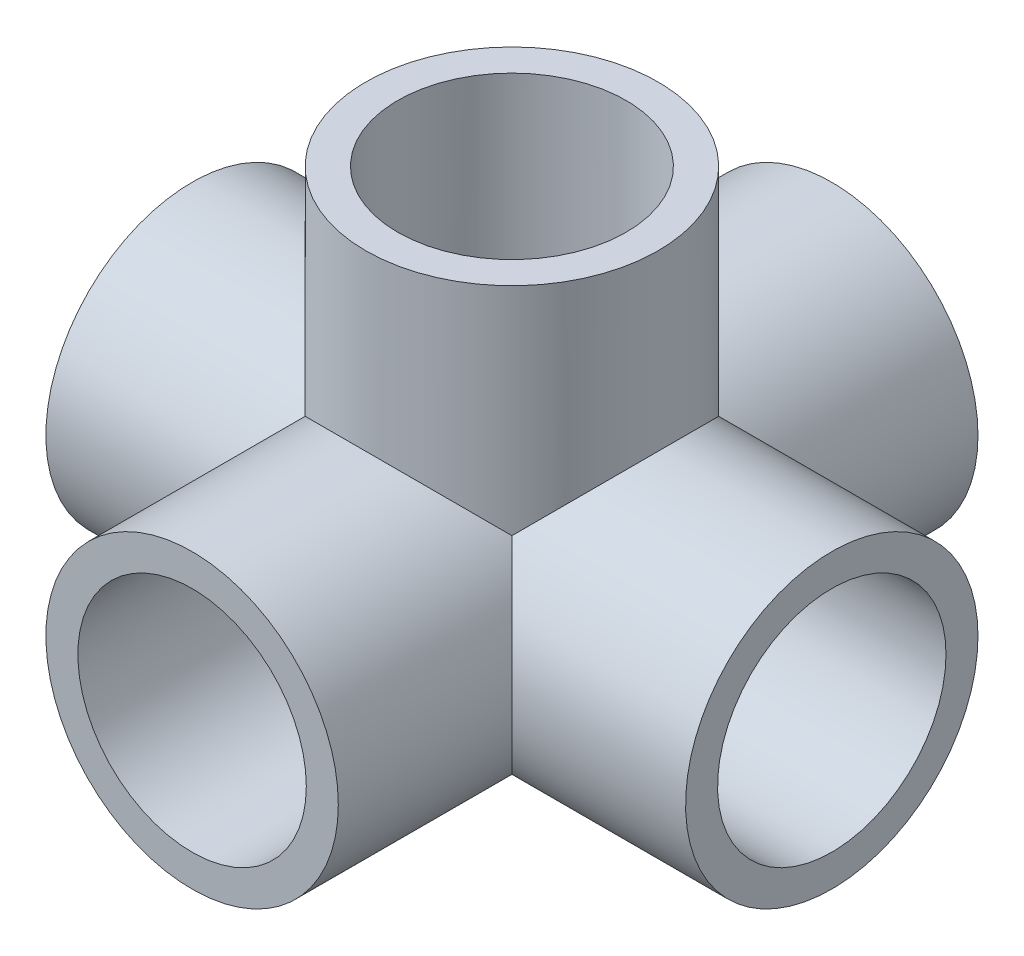
SolidWorks part; units mm, degrees
ref_plane "前视基准面" through (0, 0, 0) normal (0, 0, 1) x (1, 0, 0)
ref_plane "上视基准面" through (0, 0, 0) normal (0, 1, 0) x (1, 0, 0)
ref_plane "右视基准面" through (0, 0, 0) normal (1, 0, 0) x (0, 0, -1)
other "Configuration Table"
sketch "草图1" plane through (0, 0, 0) normal (0, 0, 1) x (1, 0, 0)
  circle A0 centre (0, 0) radius 12.5
  circle A1 centre (0, 0) radius 16
  dimension "D1" = 25
  dimension "D2" = 32
extrude "凸台-拉伸1" add sketch "草图1" along normal mid plane 70
sketch "草图2" plane through (0, 0, 0) normal (1, 0, 0) x (0, 0, -1)
  circle A0 centre (0, 0) radius 16
  circle A1 centre (0, 0) radius 12.5
  dimension "D1" = 32
  dimension "D2" = 25
extrude "凸台-拉伸2" add sketch "草图2" along normal mid plane 70
sketch "草图4" plane through (0, 0, 0) normal (0, 1, 0) x (1, 0, 0)
  circle A2 centre (0, 0) radius 16
  circle A3 centre (0, 0) radius 12.5
  dimension "D1" = 32
  dimension "D2" = 25
extrude "凸台-拉伸3" add sketch "草图4" along normal blind 35
